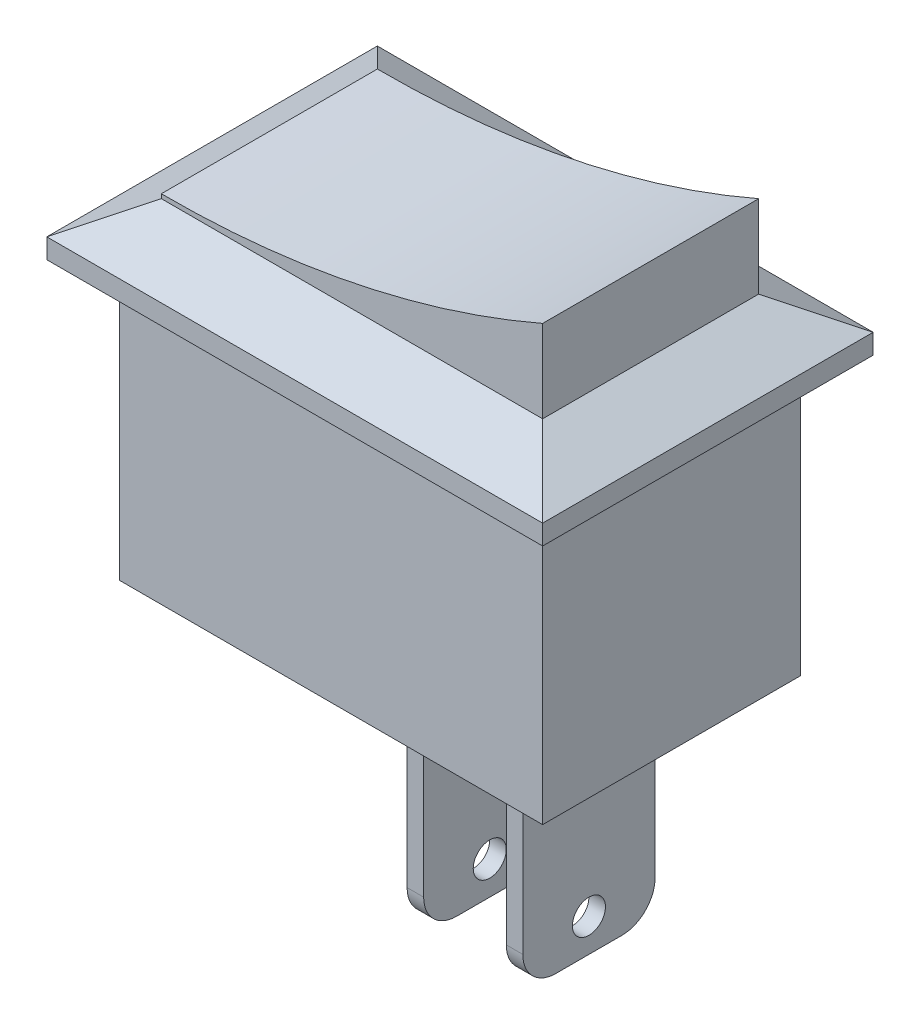
SolidWorks part; units mm, degrees
ref_plane "Front Plane" through (0, 0, 0) normal (0, 0, 1) x (1, 0, 0)
ref_plane "Top Plane" through (0, 0, 0) normal (0, 1, 0) x (1, 0, 0)
ref_plane "Right Plane" through (0, 0, 0) normal (1, 0, 0) x (0, 0, -1)
sketch "Sketch1" plane through (0, 0, 0) normal (0, 1, 0) x (1, 0, 0)
  line L1 (-7.5, -5) -> (7.5, -5)
  line L2 (-7.5, -5) -> (-7.5, 5)
  line L3 (-7.5, 5) -> (7.5, 5)
  line L4 (7.5, -5) -> (7.5, 5)
  line L5 (-7.5, -5) -> (7.5, 5) construction
  line L6 (-7.5, 5) -> (7.5, -5) construction
  point P0 (0, 0)
  dimension "D1" = 15
  dimension "D2" = 10
extrude "Boss-Extrude1" add sketch "Sketch1" along normal blind 10
sketch "Sketch2" plane through (0, 0, 0) normal (0, -1, 0) x (1, 0, 0)
  line L0 (-7.5, 5) -> (7.5, 5) construction
  line L1 (-6.4, -3.9) -> (6.4, -3.9)
  line L2 (-6.4, -3.9) -> (-6.4, 3.9)
  line L3 (-6.4, 3.9) -> (6.4, 3.9)
  line L4 (6.4, -3.9) -> (6.4, 3.9)
  line L5 (-6.4, -3.9) -> (6.4, 3.9) construction
  line L6 (-6.4, 3.9) -> (6.4, -3.9) construction
  line L7 (-7.5, -5) -> (-7.5, 5) construction
  line L9 (-7.5, -5) -> (7.5, -5)
  line L10 (-7.5, -5) -> (-7.5, 5)
  line L11 (-7.5, 5) -> (7.5, 5)
  line L12 (7.5, -5) -> (7.5, 5)
  line L13 (-7.5, -5) -> (7.5, 5) construction
  line L14 (-7.5, 5) -> (7.5, -5) construction
  point P0 (0, 0)
  point P10 (0, 0)
  dimension "D1" = 1.1
  dimension "D2" = 1.1
extrude "Cut-Extrude1" cut sketch "Sketch2" against normal blind 8.4
chamfer "Chamfer1" distance 1 angle 60 4 edges at (-7.5, 10, 0) (0, 10, 5) (7.5, 10, 0) (0, 10, -5)
sketch "Sketch3" plane through (0, 0, 0) normal (0, -1, 0) x (1, 0, 0)
  line L0 (-6.4, 2) -> (6.4, 2) construction
  line L1 (-6.4, 3.9) -> (-6.4, -3.9) construction
  line L2 (6.4, -3.9) -> (6.4, 3.9) construction
  line L3 (-6.4, 0) -> (6.4, 0) construction
  line L4 (-6.4, -2) -> (6.4, -2) construction
  line L5 (3.4, -2) -> (3.4, 2)
  line L6 (0.4, -2) -> (0.4, 2)
  dimension "D1" = 2
  dimension "D2" = 3
extrude "Extrude-Thin1" add sketch "Sketch3" along normal blind 6.6 thin
fillet "Fillet1" radius 1 4 edges at (3.65, -6.6, -2) (3.65, -6.6, 2) (0.65, -6.6, -2) (0.65, -6.6, 2)
sketch "Sketch4" plane through (0.4, 0, 0) normal (-1, 0, 0) x (0, 0, 1)
  line L0 (-2, -5.6) -> (2, -5.6) construction
  circle A0 centre (0, -5.6) radius 0.5
  dimension "D1" = 1
extrude "Cut-Extrude2" cut sketch "Sketch4" against normal blind 6.6
sketch "Sketch5" plane through (0, 10, 0) normal (0, 1, 0) x (1, 0, 0)
  line L1 (-5.7679, 3.2679) -> (5.7679, 3.2679)
  line L2 (-5.7679, 3.2679) -> (-5.7679, -3.2679)
  line L3 (-5.7679, -3.2679) -> (5.7679, -3.2679)
  line L4 (5.7679, 3.2679) -> (5.7679, -3.2679)
extrude "Boss-Extrude2" add sketch "Sketch5" along normal blind 2.5
sketch "Sketch6" plane through (0, 0, 3.2679) normal (0, 0, 1) x (1, 0, 0)
  line L0 (-5.7679, 12.5) -> (5.7679, 12.5) construction
  line L1 (-5.7679, 12.5) -> (-5.7679, 10) construction
  arc A0 (5.7679, 12.5) -> (-5.7679, 10.1288) centre (-5.6271, 38.6898) cw
  point P3 (3.9041, 12.5)
  point P7 (5.7679, 12.5)
  point P9 (-5.7679, 10)
  point P10 (-5.7679, 10.1288)
extrude "Cut-Extrude5" cut sketch "Sketch6" against normal blind 7.5 and the other way through all flip side to cut
